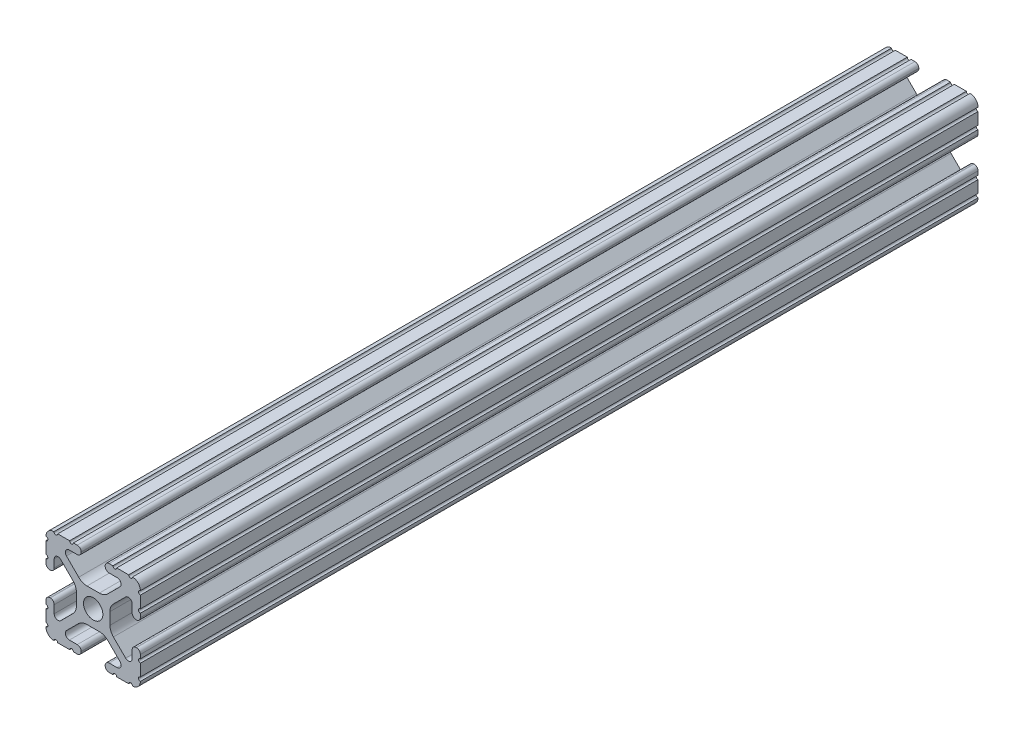
SolidWorks part; units mm, degrees
ref_plane "Front Plane" through (0, 0, 0) normal (0, 0, 1) x (1, 0, 0)
ref_plane "Top Plane" through (0, 0, 0) normal (0, 1, 0) x (1, 0, 0)
ref_plane "Right Plane" through (0, 0, 0) normal (1, 0, 0) x (0, 0, -1)
sketch "Sketch1" plane through (0, 0, 0) normal (0, 0, 1) x (1, 0, 0)
  line L88 (-7.1797, -8.6452) -> (-3.9523, -5.4237)
  line L89 (-1.7093, -4.4958) -> (1.7093, -4.4958)
  line L90 (3.9523, -5.4237) -> (7.1797, -8.6452)
  line L91 (6.4164, -10.4902) -> (4.2875, -10.4902)
  line L92 (3.2385, -11.5392) -> (3.2385, -11.651)
  line L93 (4.2875, -12.7) -> (5.3171, -12.7)
  line L94 (6.3331, -12.7) -> (9.5504, -12.7)
  line L95 (12.7, -9.5504) -> (12.7, -6.3331)
  line L96 (12.7, -5.3171) -> (12.7, -4.2875)
  line L97 (11.651, -3.2385) -> (11.5392, -3.2385)
  line L98 (10.4902, -4.2875) -> (10.4902, -6.4021)
  line L99 (8.7371, -7.1294) -> (5.441, -3.8408)
  line L100 (4.5085, -1.5932) -> (4.5085, 1.5932)
  line L101 (5.441, 3.8408) -> (8.7371, 7.1294)
  line L102 (10.4902, 6.4021) -> (10.4902, 4.2875)
  line L103 (11.5392, 3.2385) -> (11.651, 3.2385)
  line L104 (12.7, 4.2875) -> (12.7, 5.3171)
  line L105 (12.7, 6.3331) -> (12.7, 9.5504)
  line L106 (9.5504, 12.7) -> (6.3331, 12.7)
  line L107 (5.3171, 12.7) -> (4.2875, 12.7)
  line L108 (3.2385, 11.651) -> (3.2385, 11.5392)
  line L109 (4.2875, 10.4902) -> (6.4768, 10.4902)
  line L110 (7.207, 8.7244) -> (3.8983, 5.4232)
  line L111 (1.6558, 4.4958) -> (-1.6558, 4.4958)
  line L112 (-3.8983, 5.4232) -> (-7.207, 8.7244)
  line L113 (-6.4768, 10.4902) -> (-4.2875, 10.4902)
  line L114 (-3.2385, 11.5392) -> (-3.2385, 11.651)
  line L115 (-4.2875, 12.7) -> (-5.3171, 12.7)
  line L116 (-6.3331, 12.7) -> (-9.5504, 12.7)
  line L117 (-12.7, 9.5504) -> (-12.7, 6.3331)
  line L118 (-12.7, 5.3171) -> (-12.7, 4.2875)
  line L119 (-11.651, 3.2385) -> (-11.5392, 3.2385)
  line L120 (-10.4902, 4.2875) -> (-10.4902, 6.4021)
  line L121 (-8.7371, 7.1294) -> (-5.441, 3.8408)
  line L122 (-4.5085, 1.5932) -> (-4.5085, -1.5932)
  line L123 (-5.441, -3.8408) -> (-8.7371, -7.1294)
  line L124 (-10.4902, -6.4021) -> (-10.4902, -4.2875)
  line L125 (-11.5392, -3.2385) -> (-11.651, -3.2385)
  line L126 (-12.7, -4.2875) -> (-12.7, -5.3171)
  line L127 (-12.7, -6.3331) -> (-12.7, -9.5504)
  line L128 (-9.5504, -12.7) -> (-6.3331, -12.7)
  line L129 (-5.3171, -12.7) -> (-4.2875, -12.7)
  line L130 (-3.2385, -11.651) -> (-3.2385, -11.5392)
  line L131 (-4.2875, -10.4902) -> (-6.4164, -10.4902)
  circle A1 centre (0, 0) radius 2.6035
  arc A104 (-7.1797, -8.6452) -> (-6.4164, -10.4902) centre (-6.4164, -9.4098) ccw
  arc A105 (-1.7093, -4.4958) -> (-3.9523, -5.4237) centre (-1.7093, -7.6708) ccw
  arc A106 (3.9523, -5.4237) -> (1.7093, -4.4958) centre (1.7093, -7.6708) ccw
  arc A107 (6.4164, -10.4902) -> (7.1797, -8.6452) centre (6.4164, -9.4098) ccw
  arc A108 (4.2875, -10.4902) -> (3.2385, -11.5392) centre (4.2875, -11.5392) ccw
  arc A109 (3.2385, -11.651) -> (4.2875, -12.7) centre (4.2875, -11.651) ccw
  arc A110 (6.3331, -12.7) -> (5.3171, -12.7) centre (5.8251, -12.7) ccw
  arc A111 (10.5664, -12.6998) -> (9.5504, -12.7) centre (10.0584, -12.7) ccw
  arc A112 (10.5664, -12.6998) -> (12.6998, -10.5664) centre (10.5918, -10.5918) ccw
  arc A113 (12.7, -9.5504) -> (12.6998, -10.5664) centre (12.7, -10.0584) ccw
  arc A114 (12.7, -5.3171) -> (12.7, -6.3331) centre (12.7, -5.8251) ccw
  arc A115 (12.7, -4.2875) -> (11.651, -3.2385) centre (11.651, -4.2875) ccw
  arc A116 (11.5392, -3.2385) -> (10.4902, -4.2875) centre (11.5392, -4.2875) ccw
  arc A117 (8.7371, -7.1294) -> (10.4902, -6.4021) centre (9.4628, -6.4021) ccw
  arc A118 (4.5085, -1.5932) -> (5.441, -3.8408) centre (7.6835, -1.5932) ccw
  arc A119 (5.441, 3.8408) -> (4.5085, 1.5932) centre (7.6835, 1.5932) ccw
  arc A120 (10.4902, 6.4021) -> (8.7371, 7.1294) centre (9.4628, 6.4021) ccw
  arc A121 (10.4902, 4.2875) -> (11.5392, 3.2385) centre (11.5392, 4.2875) ccw
  arc A122 (11.651, 3.2385) -> (12.7, 4.2875) centre (11.651, 4.2875) ccw
  arc A123 (12.7, 6.3331) -> (12.7, 5.3171) centre (12.7, 5.8251) ccw
  arc A124 (12.6998, 10.5664) -> (12.7, 9.5504) centre (12.7, 10.0584) ccw
  arc A125 (12.6998, 10.5664) -> (10.5664, 12.6998) centre (10.5918, 10.5918) ccw
  arc A126 (9.5504, 12.7) -> (10.5664, 12.6998) centre (10.0584, 12.7) ccw
  arc A127 (5.3171, 12.7) -> (6.3331, 12.7) centre (5.8251, 12.7) ccw
  arc A128 (4.2875, 12.7) -> (3.2385, 11.651) centre (4.2875, 11.651) ccw
  arc A129 (3.2385, 11.5392) -> (4.2875, 10.4902) centre (4.2875, 11.5392) ccw
  arc A130 (7.207, 8.7244) -> (6.4768, 10.4902) centre (6.4768, 9.4563) ccw
  arc A131 (1.6558, 4.4958) -> (3.8983, 5.4232) centre (1.6558, 7.6708) ccw
  arc A132 (-3.8983, 5.4232) -> (-1.6558, 4.4958) centre (-1.6558, 7.6708) ccw
  arc A133 (-6.4768, 10.4902) -> (-7.207, 8.7244) centre (-6.4768, 9.4563) ccw
  arc A134 (-4.2875, 10.4902) -> (-3.2385, 11.5392) centre (-4.2875, 11.5392) ccw
  arc A135 (-3.2385, 11.651) -> (-4.2875, 12.7) centre (-4.2875, 11.651) ccw
  arc A136 (-6.3331, 12.7) -> (-5.3171, 12.7) centre (-5.8251, 12.7) ccw
  arc A137 (-10.5664, 12.6998) -> (-9.5504, 12.7) centre (-10.0584, 12.7) ccw
  arc A138 (-10.5664, 12.6998) -> (-12.6998, 10.5664) centre (-10.5918, 10.5918) ccw
  arc A139 (-12.7, 9.5504) -> (-12.6998, 10.5664) centre (-12.7, 10.0584) ccw
  arc A140 (-12.7, 5.3171) -> (-12.7, 6.3331) centre (-12.7, 5.8251) ccw
  arc A141 (-12.7, 4.2875) -> (-11.651, 3.2385) centre (-11.651, 4.2875) ccw
  arc A142 (-11.5392, 3.2385) -> (-10.4902, 4.2875) centre (-11.5392, 4.2875) ccw
  arc A143 (-8.7371, 7.1294) -> (-10.4902, 6.4021) centre (-9.4628, 6.4021) ccw
  arc A144 (-4.5085, 1.5932) -> (-5.441, 3.8408) centre (-7.6835, 1.5932) ccw
  arc A145 (-5.441, -3.8408) -> (-4.5085, -1.5932) centre (-7.6835, -1.5932) ccw
  arc A146 (-10.4902, -6.4021) -> (-8.7371, -7.1294) centre (-9.4628, -6.4021) ccw
  arc A147 (-10.4902, -4.2875) -> (-11.5392, -3.2385) centre (-11.5392, -4.2875) ccw
  arc A148 (-11.651, -3.2385) -> (-12.7, -4.2875) centre (-11.651, -4.2875) ccw
  arc A149 (-12.7, -6.3331) -> (-12.7, -5.3171) centre (-12.7, -5.8251) ccw
  arc A150 (-12.6998, -10.5664) -> (-12.7, -9.5504) centre (-12.7, -10.0584) ccw
  arc A151 (-12.6998, -10.5664) -> (-10.5664, -12.6998) centre (-10.5918, -10.5918) ccw
  arc A152 (-9.5504, -12.7) -> (-10.5664, -12.6998) centre (-10.0584, -12.7) ccw
  arc A153 (-5.3171, -12.7) -> (-6.3331, -12.7) centre (-5.8251, -12.7) ccw
  arc A154 (-4.2875, -12.7) -> (-3.2385, -11.651) centre (-4.2875, -11.651) ccw
  arc A155 (-3.2385, -11.5392) -> (-4.2875, -10.4902) centre (-4.2875, -11.5392) ccw
extrude "Boss-Extrude1" add sketch "Sketch1" along normal mid plane 1219.2
sketch "Sketch2" plane through (-0.7939, -0.7957, 0) normal (-0.7063, -0.7079, 0) x (0.7079, -0.7063, 0)
  line L0 (30.9144, 384.1228) -> (-21.6694, 384.1228)
  line L1 (-21.6694, 384.1228) -> (-21.6694, -615.8042)
  line L2 (-21.6694, -615.8042) -> (30.9144, -615.8042)
  line L3 (30.9144, -615.8042) -> (30.9144, 384.1228)
extrude "Cut-Extrude1" cut sketch "Sketch2" against normal blind 22.352 and the other way blind 21.082
